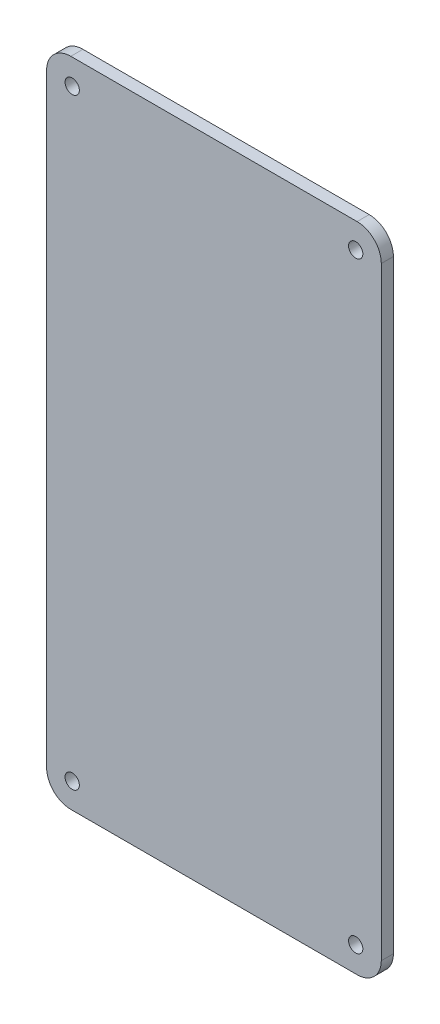
SolidWorks part; units mm, degrees
ref_plane "Front Plane" through (0, 0, 0) normal (0, 0, 1) x (1, 0, 0)
ref_plane "Top Plane" through (0, 0, 0) normal (0, 1, 0) x (1, 0, 0)
ref_plane "Right Plane" through (0, 0, 0) normal (1, 0, 0) x (0, 0, -1)
sketch "Sketch1" plane through (0, 0, 0) normal (0, 0, 1) x (1, 0, 0)
  line L1 (-30.045, -68.4476) -> (30.045, -68.4476)
  line L2 (-35.1251, -63.3675) -> (-35.1251, 63.3675)
  line L3 (-30.045, 68.4476) -> (30.045, 68.4476)
  line L4 (35.125, -63.3675) -> (35.125, 63.3675)
  line L5 (-35.1251, -68.4476) -> (35.125, 68.4476) construction
  line L6 (-35.1251, 68.4476) -> (35.125, -68.4476) construction
  arc A0 (-30.045, -68.4476) -> (-35.1251, -63.3675) centre (-30.0451, -63.3676) cw
  arc A1 (30.045, -68.4476) -> (35.125, -63.3675) centre (30.045, -63.3676) ccw
  arc A2 (30.045, 68.4476) -> (35.125, 63.3675) centre (30.045, 63.3676) cw
  arc A3 (-35.1251, 63.3675) -> (-30.045, 68.4476) centre (-30.0451, 63.3676) cw
  point P0 (0, 0)
  dimension "D3" = 5.08
  dimension "D1" = 70.2501
  dimension "D2" = 136.8951
extrude "Boss-Extrude1" add sketch "Sketch1" along normal blind 2.54
sketch "Sketch2" plane through (0, 0, 2.54) normal (0, 0, 1) x (1, 0, 0)
  line L1 (-29.75, -63.1515) -> (29.75, -63.1515) construction
  line L2 (-29.75, -63.1515) -> (-29.75, 63.1515) construction
  line L3 (-29.75, 63.1515) -> (29.75, 63.1515) construction
  line L4 (29.75, -63.1515) -> (29.75, 63.1515) construction
  line L5 (-29.75, -63.1515) -> (29.75, 63.1515) construction
  line L6 (-29.75, 63.1515) -> (29.75, -63.1515) construction
  circle A0 centre (-29.75, 63.1515) radius 1.5
  circle A1 centre (29.75, 63.1515) radius 1.5
  circle A2 centre (29.75, -63.1515) radius 1.5
  circle A3 centre (-29.75, -63.1515) radius 1.5
  point P0 (0, 0)
  dimension "D3" = 3
  dimension "D4" = 3
  dimension "D5" = 3
  dimension "D6" = 3
  dimension "D1" = 59.5
  dimension "D2" = 126.303
extrude "Cut-Extrude1" cut sketch "Sketch2" against normal through all
